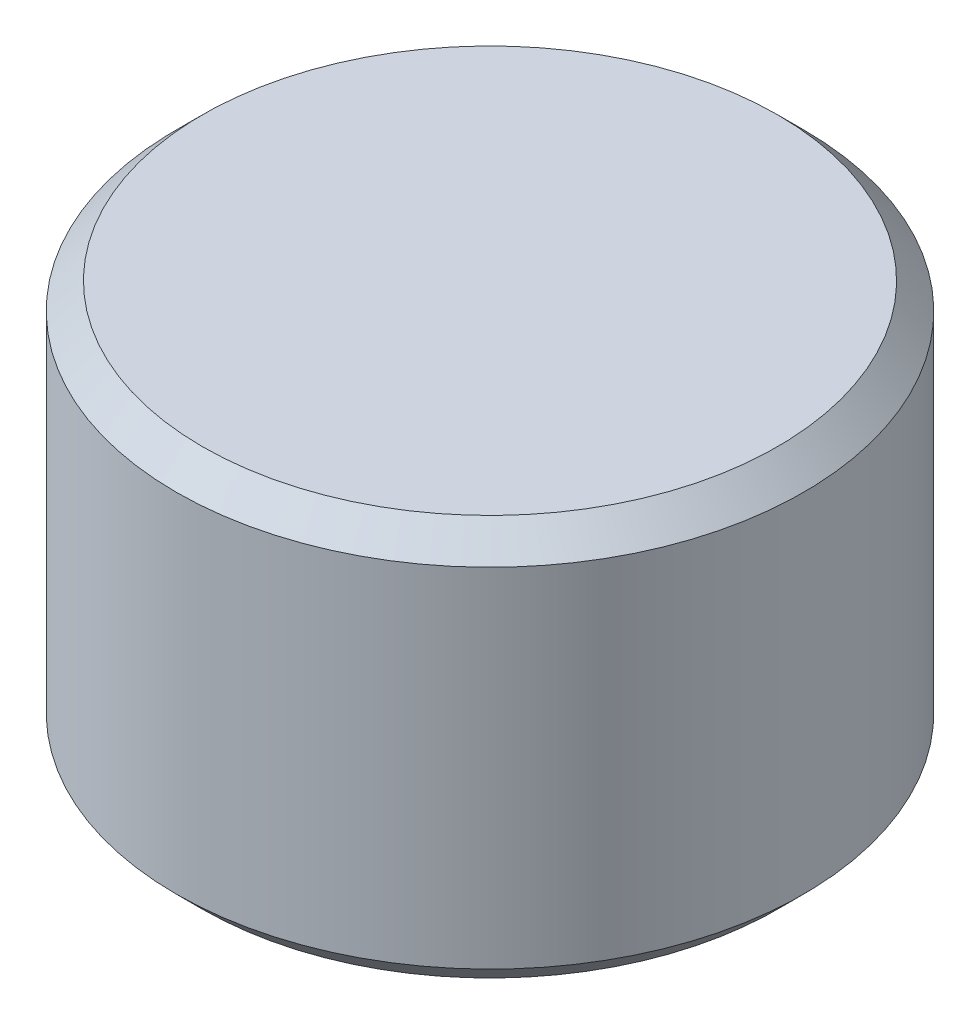
SolidWorks part; units mm, degrees
ref_plane "Front Plane" through (0, 0, 0) normal (0, 0, 1) x (1, 0, 0)
ref_plane "Top Plane" through (0, 0, 0) normal (0, 1, 0) x (1, 0, 0)
ref_plane "Right Plane" through (0, 0, 0) normal (1, 0, 0) x (0, 0, -1)
sketch "Sketch1" plane through (0, 0, 0) normal (0, 1, 0) x (1, 0, 0)
  circle A0 centre (0, 0) radius 1193.8
  dimension "D1" = 2387.6
extrude "Boss-Extrude1" add sketch "Sketch1" along normal blind 1524
sketch "Sketch2" plane through (0, 0, 0) normal (0, 0, 1) x (1, 0, 0)
  line L0 (-1193.8, 508) -> (-1193.8, 0)
  line L1 (-1193.8, 1524) -> (-1193.8, 0) construction
  line L2 (-1193.8, 0) -> (-558.8, 0)
  line L3 (-1193.8, 0) -> (1193.8, 0) construction
  line L4 (-558.8, 0) -> (-1193.8, 508)
  line L5 (0, 0) -> (0, 258.9927) construction
  line L6 (558.8, 0) -> (1193.8, 508)
  dimension "D1" = 508
  dimension "D2" = 635
chamfer "Chamfer1" distance 100 angle 45 1 edges at (0, 1524, 1193.8)
chamfer "Chamfer2" distance 100 angle 45 1 edges at (0, 0, 1193.8)
